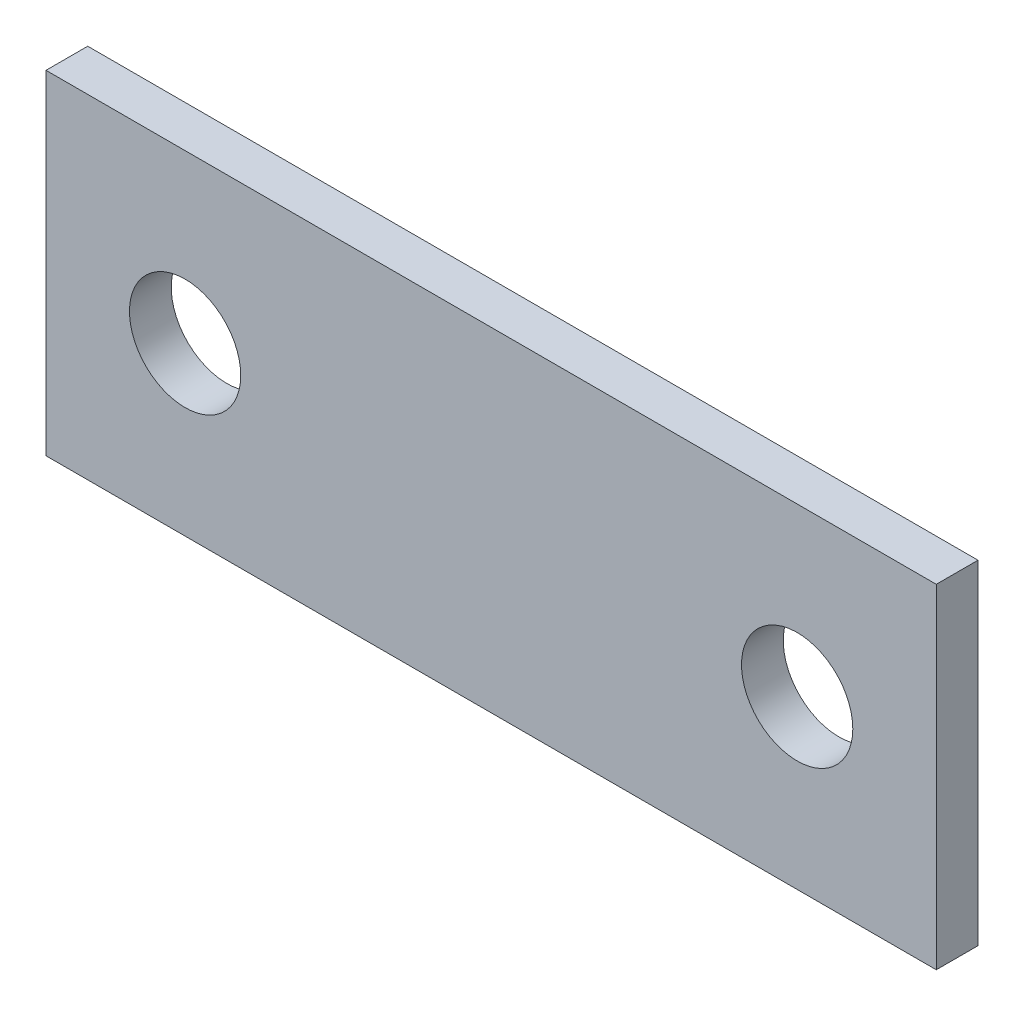
SolidWorks part; units mm, degrees
ref_plane "Front" through (0, 0, 0) normal (0, 0, 1) x (1, 0, 0)
ref_plane "Top" through (0, 0, 0) normal (0, 1, 0) x (1, 0, 0)
ref_plane "Right" through (0, 0, 0) normal (1, 0, 0) x (0, 0, -1)
sketch "Sketch1" plane through (0, 0, 0) normal (0, 0, 1) x (1, 0, 0)
  line L0 (17.4625, 0) -> (-17.4625, 0) construction
  line L1 (25.4, -9.525) -> (-25.4, -9.525)
  line L2 (25.4, -9.525) -> (25.4, 9.525)
  line L3 (25.4, 9.525) -> (-25.4, 9.525)
  line L4 (-25.4, -9.525) -> (-25.4, 9.525)
  line L5 (25.4, -9.525) -> (-25.4, 9.525) construction
  line L6 (25.4, 9.525) -> (-25.4, -9.525) construction
  circle A0 centre (-17.4625, 0) radius 3.175
  circle A1 centre (17.4625, 0) radius 3.175
  point P0 (0, 0)
  dimension "Hole Size" = 6.35
  dimension "Length" = 50.8
  dimension "Width" = 19.05
  dimension "Center to Center " = 34.925
extrude "Boss-Extrude1" add sketch "Sketch1" along normal blind 2.3813
